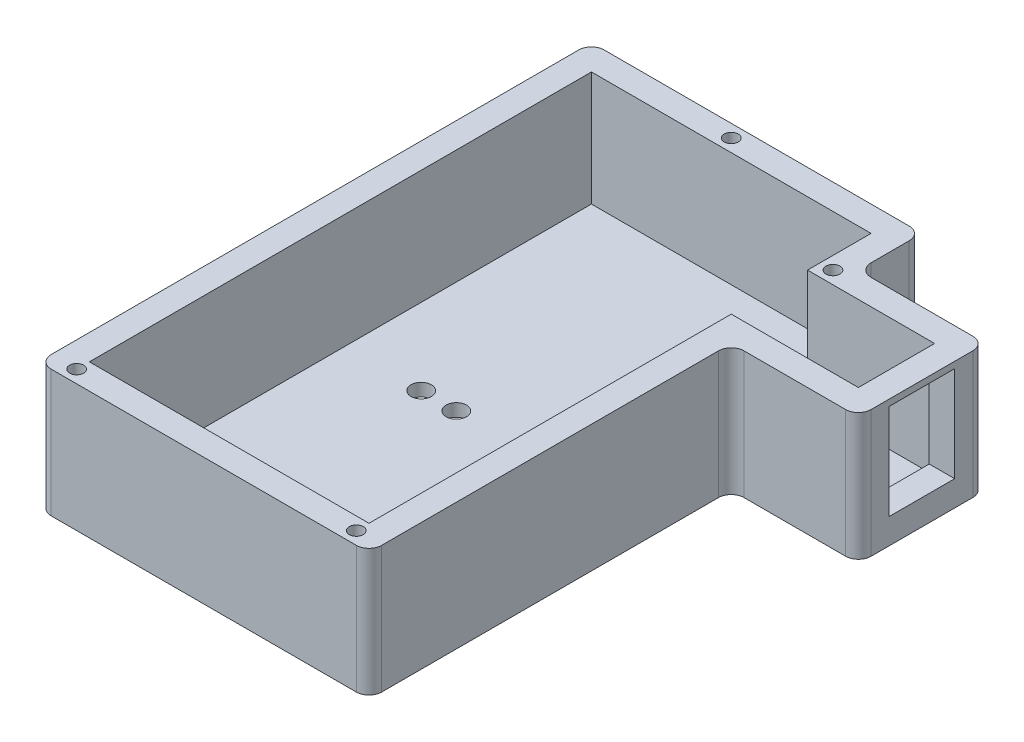
SolidWorks part; units mm, degrees
ref_plane "Front Plane" through (0, 0, 0) normal (0, 0, 1) x (1, 0, 0)
ref_plane "Top Plane" through (0, 0, 0) normal (0, 1, 0) x (1, 0, 0)
ref_plane "Right Plane" through (0, 0, 0) normal (1, 0, 0) x (0, 0, -1)
sketch "Sketch1" plane through (0, 0, 0) normal (0, 1, 0) x (1, 0, 0)
  line L0 (52, 77) -> (52, 87)
  line L1 (0, 0) -> (52, 0)
  line L2 (0, 0) -> (0, 87)
  line L3 (0, 87) -> (52, 87)
  line L4 (52, 0) -> (52, 57)
  line L5 (52, 77) -> (72, 77)
  line L7 (52, 57) -> (72, 57)
  line L8 (72, 77) -> (72, 57)
  dimension "D1" = 52
  dimension "D2" = 87
  dimension "D3" = 20
  dimension "D4" = 20
  dimension "D5" = 10
extrude "Boss-Extrude1" add sketch "Sketch1" along normal blind 20
sketch "Sketch2" plane through (0, 20, 0) normal (0, 1, 0) x (1, 0, 0)
  line L0 (0, 87) -> (0, 0) construction
  line L1 (4, 83) -> (48, 83)
  line L2 (4, 83) -> (4, 4)
  line L3 (4, 4) -> (48, 4)
  line L4 (48, 83) -> (48, 4)
  line L5 (0, 0) -> (52, 0) construction
  point P4 (4, 43.5)
  point P7 (0, 43.5)
  point P8 (26, 4)
  point P11 (26, 0)
  dimension "D1" = 44
  dimension "D2" = 79
extrude "battery cut" cut sketch "Sketch2" against normal blind 18
sketch "Sketch3" plane through (0, 20, 0) normal (0, 1, 0) x (1, 0, 0)
  line L0 (48, 4) -> (48, 83) construction
  line L1 (48, 73) -> (68, 73)
  line L2 (48, 73) -> (48, 61)
  line L3 (48, 61) -> (68, 61)
  line L4 (68, 73) -> (68, 61)
  line L5 (72, 77) -> (52, 77) construction
  line L6 (72, 57) -> (72, 77) construction
  dimension "D1" = 4
  dimension "D2" = 4
  dimension "D3" = 12
extrude "Cut-Extrude2" cut sketch "Sketch3" against normal blind 18
sketch "Sketch4" plane through (0, 20, 0) normal (0, 1, 0) x (1, 0, 0)
  line L0 (0, 87) -> (0, 0) construction
  line L2 (4, 4) -> (48, 4) construction
  line L6 (0, 0) -> (52, 0) construction
  line L7 (52, 0) -> (52, 57) construction
  line L8 (52, 87) -> (0, 87) construction
  line L9 (52, 77) -> (52, 87) construction
  line L10 (72, 77) -> (52, 77) construction
  circle A0 centre (4, 2) radius 1.1
  circle A1 centre (48, 2) radius 1.1
  circle A2 centre (24, 85) radius 1.1
  circle A3 centre (50, 75) radius 1.1
  dimension "D1" = 4
  dimension "D8" = 2.2
  dimension "D9" = 2.2
  dimension "D10" = 2.2
  dimension "D11" = 2.2
  dimension "D12" = 2
  dimension "D2" = 2
  dimension "D3" = 4
  dimension "D4" = 2
  dimension "D5" = 24
  dimension "D6" = 2
  dimension "D7" = 2
extrude "nut holes" cut sketch "Sketch4" against normal blind 10
sketch "Sketch5" plane through (72, 0, 0) normal (1, 0, 0) x (0, 0, -1)
  line L0 (57, 0) -> (77, 0) construction
  line L1 (61.85, 19) -> (72.15, 19)
  line L2 (61.85, 19) -> (61.85, 4)
  line L3 (61.85, 4) -> (72.15, 4)
  line L4 (72.15, 19) -> (72.15, 4)
  line L5 (57, 20) -> (77, 20) construction
  point P8 (67, 19)
  point P9 (67, 20)
  dimension "D1" = 10.3
  dimension "D2" = 15
  dimension "D3" = 4
  dimension "D4" = 1
extrude "Cut-Extrude4" cut sketch "Sketch5" against normal blind 5
sketch "Sketch6" plane through (0, 2, 0) normal (0, 1, 0) x (1, 0, 0)
  line L0 (48, 4) -> (48, 61) construction
  line L1 (48, 4) -> (48, 61) construction
  line L3 (48, 83) -> (4, 83) construction
  circle A0 centre (21.56, 44.18) radius 1.6
  circle A1 centre (43.53, 44.18) radius 1.6
  circle A2 centre (38, 44.18) radius 1.6
  circle A3 centre (16.03, 44.18) radius 1.6
  dimension "D1" = 4.47
  dimension "D2" = 26.44
  dimension "D3" = 38.82
  dimension "D4" = 10
  dimension "D5" = 21.97
extrude "Cut-Extrude5" cut sketch "Sketch6" against normal blind 6
fillet "Fillet1" radius 2 8 edges at (0, 10, 0) (0, 10, -87) (52, 10, -87) (52, 10, -77) (72, 10, -77) (72, 10, -57) (52, 10, -57) (52, 10, 0)
